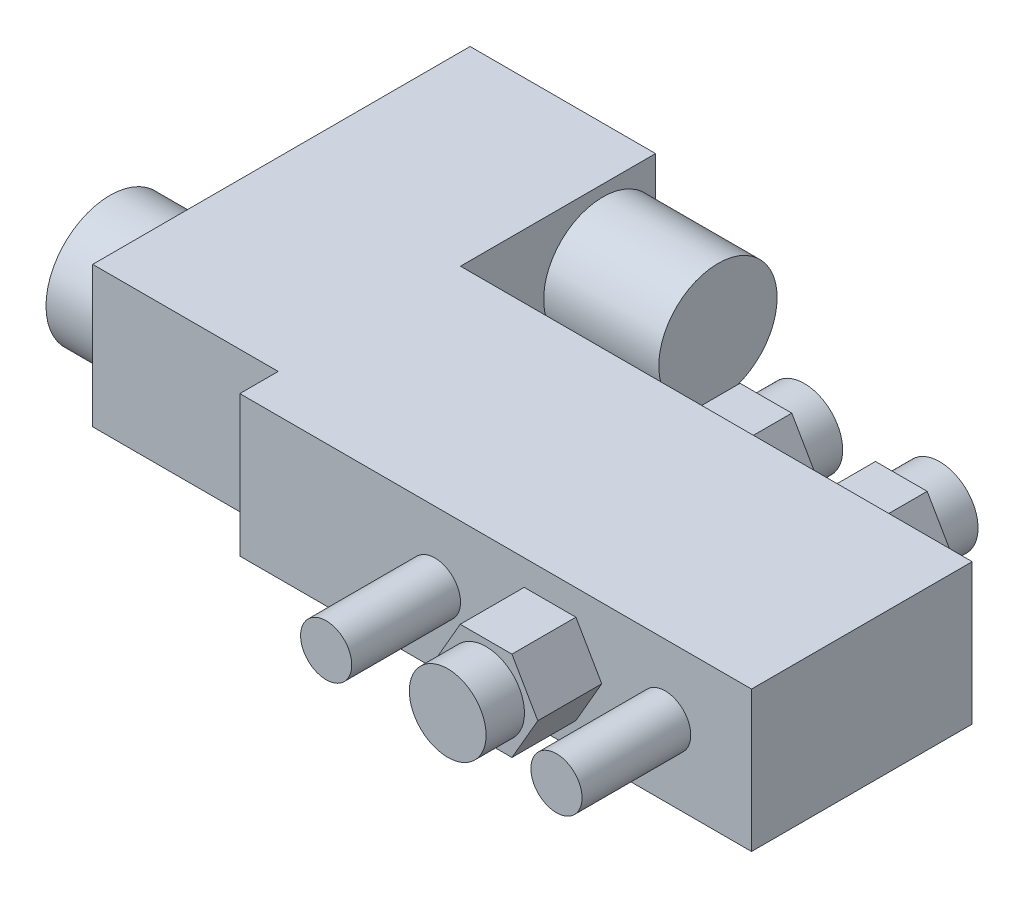
SolidWorks part; units mm, degrees
ref_plane "Front Plane" through (0, 0, 0) normal (0, 0, 1) x (1, 0, 0)
ref_plane "Top Plane" through (0, 0, 0) normal (0, 1, 0) x (1, 0, 0)
ref_plane "Right Plane" through (0, 0, 0) normal (1, 0, 0) x (0, 0, -1)
sketch "Sketch1" plane through (0, 0, 0) normal (0, 1, 0) x (1, 0, 0)
  line L0 (0, 0) -> (80, 0)
  line L1 (80, 0) -> (80, 34.5)
  line L3 (0, 6) -> (0, 0)
  line L22 (0, 6) -> (-29, 6)
  line L23 (0, 34.5) -> (0, 65)
  line L24 (0, 65) -> (-29, 65)
  line L39 (-29, 6) -> (-29, 65)
  line L41 (80, 34.5) -> (0, 34.5)
  point P4 (0, 0)
  point P6 (0, 63.6234)
  dimension "D1" = 80
  dimension "D2" = 34.5
  dimension "D3" = 29
  dimension "D4" = 59
  dimension "D5" = 6
extrude "Boss-Extrude1" add sketch "Sketch1" along normal blind 22
sketch "Sketch2" plane through (0, 0, 0) normal (0, 0, 1) x (1, 0, 0)
  line L0 (0, 22) -> (0, 0) construction
  line L2 (80, 22) -> (80, 0) construction
  circle A0 centre (30.5, 11) radius 4
  circle A2 centre (66.5, 11) radius 4
  point P2 (0, 0)
  point P7 (0, 11)
  dimension "D1" = 8
  dimension "D2" = 28
  dimension "D3" = 9.5
extrude "Boss-Extrude2" add sketch "Sketch2" along normal blind 17
sketch "Sketch3" plane through (0, 0, -34.5) normal (0, 0, -1) x (-1, 0, 0)
  line L0 (-80, 22) -> (-80, 0) construction
  line L1 (-50.8342, 11) -> (-54.8756, 18)
  line L2 (-54.8756, 18) -> (-62.9585, 18)
  line L3 (-62.9585, 18) -> (-67, 11)
  line L4 (-67, 11) -> (-62.9585, 4)
  line L5 (-62.9585, 4) -> (-54.8756, 4)
  line L6 (-54.8756, 4) -> (-50.8342, 11)
  line L7 (-29.6684, 11) -> (-33.7098, 18)
  line L8 (-33.7098, 18) -> (-41.7927, 18)
  line L9 (-41.7927, 18) -> (-45.8342, 11)
  line L10 (-45.8342, 11) -> (-41.7927, 4)
  line L11 (-41.7927, 4) -> (-33.7098, 4)
  line L12 (-33.7098, 4) -> (-29.6684, 11)
  line L13 (-80, 0) -> (0, 0) construction
  circle A2 centre (-58.9171, 11) radius 7 construction
  circle A3 centre (-37.7513, 11) radius 7 construction
  point P9 (0, 0)
  point P19 (-80, 11)
  point P22 (-35.813, 11)
  dimension "D1" = 14
  dimension "D2" = 13
  dimension "D3" = 5
extrude "Boss-Extrude3" add sketch "Sketch3" along normal blind 10
sketch "Sketch4" plane through (0, 0, 0) normal (1, 0, 0) x (0, 0, -1)
  line L0 (34.5, 22) -> (34.5, 0) construction
  line L1 (65, 22) -> (65, 0) construction
  circle A0 centre (56.75, 11) radius 9.25
  point P4 (0, 0)
  point P7 (65, 11)
  dimension "D1" = 18.5
  dimension "D2" = 13
extrude "Boss-Extrude4" add sketch "Sketch4" along normal blind 18
sketch "Sketch5" plane through (-29, 0, 0) normal (-1, 0, 0) x (0, 0, 1)
  line L0 (-6, 22) -> (-6, 0) construction
  circle A0 centre (-17.7, 11) radius 10
  point P2 (0, 0)
  point P5 (-6, 11)
  dimension "D1" = 20
  dimension "D2" = 1.7
extrude "Boss-Extrude5" add sketch "Sketch5" along normal blind 9
sketch "Sketch6" plane through (0, 0, 0) normal (0, 0, 1) x (1, 0, 0)
  line L0 (80, 22) -> (80, 0) construction
  line L1 (56.5829, 11) -> (52.5415, 18)
  line L2 (52.5415, 18) -> (44.4585, 18)
  line L3 (44.4585, 18) -> (40.4171, 11)
  line L4 (40.4171, 11) -> (44.4585, 4)
  line L5 (44.4585, 4) -> (52.5415, 4)
  line L6 (52.5415, 4) -> (56.5829, 11)
  line L7 (0, 22) -> (80, 22) construction
  line L8 (30.5, 11) -> (66.5, 11) construction
  circle A0 centre (48.5, 11) radius 7 construction
  point P1 (48.5, 11)
  point P11 (80, 11)
  dimension "D1" = 14
extrude "Boss-Extrude6" add sketch "Sketch6" along normal blind 10
sketch "Sketch7" plane through (0, 0, 10) normal (0, 0, 1) x (1, 0, 0)
  line L0 (44.4585, 4) -> (52.5415, 18) construction
  line L2 (56.5829, 11) -> (52.5415, 18) construction
  circle A0 centre (48.5, 11) radius 6
  point P6 (48.5, 11)
  dimension "D1" = 1
extrude "Boss-Extrude7" add sketch "Sketch7" along normal blind 6
sketch "Sketch8" plane through (0, 0, -44.5) normal (0, 0, -1) x (-1, 0, 0)
  line L0 (-67, 11) -> (-50.8342, 11) construction
  line L1 (-45.8342, 11) -> (-29.6684, 11) construction
  line L3 (-50.8342, 11) -> (-54.8756, 18) construction
  circle A0 centre (-58.9171, 11) radius 6
  circle A1 centre (-37.7513, 11) radius 6
  dimension "D1" = 1
extrude "Boss-Extrude8" add sketch "Sketch8" along normal blind 6
